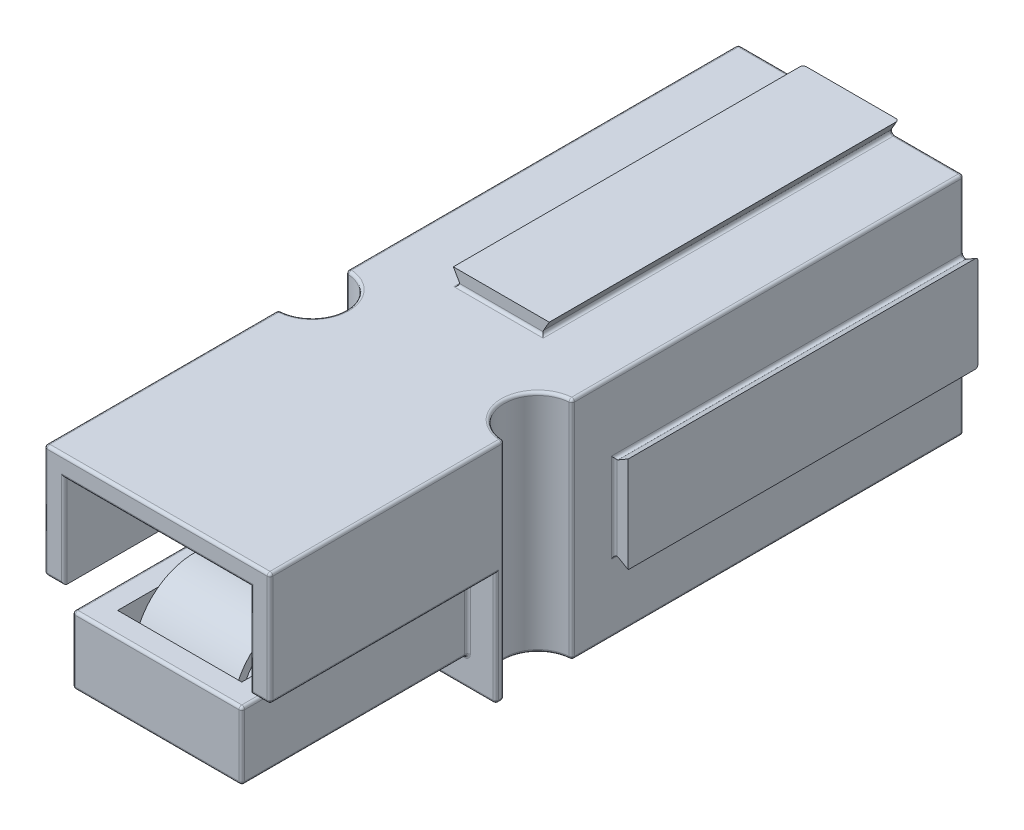
SolidWorks part; units mm, degrees
ref_plane "Face" through (0, 0, 0) normal (0, 0, 1) x (1, 0, 0)
ref_plane "Dessus" through (0, 0, 0) normal (0, 1, 0) x (1, 0, 0)
ref_plane "Droite" through (0, 0, 0) normal (1, 0, 0) x (0, 0, -1)
sketch "Esquisse1" plane through (0, 0, 0) normal (0, 0, 1) x (1, 0, 0)
  line L1 (-4.25, 4.25) -> (4.25, 4.25)
  line L2 (-4.25, 4.25) -> (-4.25, -4.25)
  line L3 (-4.25, -4.25) -> (4.25, -4.25)
  line L4 (4.25, 4.25) -> (4.25, -4.25)
  point P4 (0, 4.25)
  point P6 (-4.25, 0)
  dimension "D1" = 8.5
  dimension "D2" = 8.5
extrude "Extrusion1" add sketch "Esquisse1" along normal blind 24.6
sketch "Esquisse6" plane through (0, 0, 24.6) normal (0, 0, 1) x (1, 0, 0)
  line L0 (-4.25, 4.25) -> (-4.25, -4.25) construction
  line L2 (4.5005, 4.25) -> (4.5005, 3.75)
  line L3 (-4.25, 4.25) -> (-1.95, 4.25)
  line L4 (-4.25, 4.25) -> (-4.25, 3.75)
  line L5 (-4.25, 3.75) -> (-1.95, 3.75)
  line L6 (-1.95, 4.25) -> (-1.95, 3.75)
  line L7 (4.5005, 4.25) -> (1.45, 4.25)
  line L8 (1.45, 4.25) -> (1.45, 3.75)
  line L9 (4.5005, 3.75) -> (1.45, 3.75)
  dimension "D1" = 3.4
  dimension "D2" = 0.5
  dimension "D3" = 2.3
extrude "Enlèv. mat.-Extru.4" cut sketch "Esquisse6" against normal through all
sketch "Esquisse2" plane through (0, 0, 24.6) normal (0, 0, 1) x (1, 0, 0)
  line L0 (1.45, 4.25) -> (-1.95, 4.25) construction
  line L2 (-4.25, -4.25) -> (4.25, -4.25) construction
  line L8 (4.25, 1.45) -> (4.25, 4.25)
  line L12 (4.25, 4.25) -> (3.75, 4.25)
  line L13 (4.25, -4.25) -> (3.75, -4.25)
  line L14 (4.25, -4.25) -> (4.25, -1.95)
  line L15 (4.25, -1.95) -> (3.75, -1.95)
  line L16 (3.75, -4.25) -> (3.75, -1.95)
  line L18 (4.25, 1.45) -> (3.75, 1.45)
  line L19 (3.75, 4.25) -> (3.75, 1.45)
  dimension "D1" = 2.3
  dimension "D3" = 0.5
  dimension "D4" = 3.4
extrude "Enlèv. mat.-Extru.1" cut sketch "Esquisse2" against normal through all
sketch "Esquisse4" plane through (0, 3.75, 0) normal (0, 1, 0) x (-1, 0, 0)
  line L0 (0.25, 24.6) -> (0.25, 9.1927) construction
  line L6 (4.25, 24.6) -> (1.95, 24.6) construction
  circle A0 centre (-3.75, 15.1) radius 1.2
  circle A1 centre (4.25, 15.1) radius 1.2
  dimension "D1" = 2.4
  dimension "D2" = 9.5
extrude "Enlèv. mat.-Extru.3" cut sketch "Esquisse4" against normal through all
sketch "Esquisse11" plane through (0, 0, 24.6) normal (0, 0, 1) x (1, 0, 0)
  line L1 (-1.95, 4.25) -> (1.45, 4.25)
  line L2 (-1.95, 4.25) -> (-1.95, 3.75)
  line L3 (-1.95, 3.75) -> (1.45, 3.75)
  line L4 (1.45, 4.25) -> (1.45, 3.75)
  line L5 (4.25, 1.45) -> (3.75, 1.45)
  line L6 (4.25, 1.45) -> (4.25, -1.95)
  line L7 (4.25, -1.95) -> (3.75, -1.95)
  line L8 (3.75, 1.45) -> (3.75, -1.95)
extrude "Enlèv. mat.-Extru.9" cut sketch "Esquisse11" against normal blind 12.2
sketch "Esquisse5" plane through (0, 0, 24.6) normal (0, 0, 1) x (1, 0, 0)
  line L0 (-0.25, 3.75) -> (-0.25, -5.3524) construction
  line L1 (-4.25, -4.25) -> (3.75, -4.25) construction
  line L2 (-4.25, -0.25) -> (-3.25, -0.25)
  line L3 (-4.25, 3.75) -> (-4.25, -4.25) construction
  line L4 (-3.25, -0.25) -> (-3.25, -3.25)
  line L5 (-3.25, -3.25) -> (2.75, -3.25)
  line L6 (-4.25, 3.75) -> (3.75, 3.75) construction
  line L7 (-4.25, -0.25) -> (-4.25, -4.25)
  line L8 (-4.25, -4.25) -> (3.75, -4.25) construction
  line L9 (-4.25, -4.25) -> (3.75, -4.25) construction
  line L10 (2.75, -0.25) -> (2.75, -3.25)
  line L11 (3.75, -0.25) -> (2.75, -0.25)
  line L12 (3.75, -0.25) -> (3.75, -4.25)
  line L13 (-4.25, -4.25) -> (3.75, -4.25)
  point P19 (-0.25, -3.25)
  point P22 (-0.25, -4.25)
  dimension "D1" = 1
  dimension "D2" = 1
  dimension "D3" = 4
extrude "Enlèv. mat.-Extru.5" cut sketch "Esquisse5" against normal blind 8
sketch "Esquisse7" plane through (0, 0, 24.6) normal (0, 0, 1) x (1, 0, 0)
  line L5 (2.75, -0.85) -> (-3.25, -0.85)
  line L8 (-4.25, 3.05) -> (3.75, 3.05)
  line L9 (-3.55, 3.05) -> (3.05, 3.05)
  line L11 (-3.55, 3.75) -> (-3.55, -0.25)
  line L12 (3.05, -0.85) -> (-3.55, -0.85)
  line L24 (-3.55, 3.05) -> (-3.55, -0.85)
  line L26 (3.05, 3.75) -> (3.05, -0.25)
  line L27 (3.05, 3.05) -> (3.05, -0.85)
  dimension "D1" = 0.7
  dimension "D2" = 2.4
  dimension "D3" = 0.7
  dimension "D4" = 0.7
extrude "Enlèv. mat.-Extru.6" cut sketch "Esquisse7" against normal up to surface (8 mm away) up to face at (-0.25, -2, 16.6)
sketch "Esquisse8" plane through (0, 0, 0) normal (0, 0, -1) x (-1, 0, 0)
  line L37 (2.85, 3.75) -> (2.85, -4.25)
  line L38 (2.85, 2.35) -> (2.85, -2.85)
  line L40 (-2.35, -1.95) -> (-2.35, -4.25)
  line L41 (-2.35, 2.35) -> (-2.35, -2.85)
  line L43 (4.25, -2.85) -> (-3.75, -2.85)
  line L44 (2.85, -2.85) -> (-2.35, -2.85)
  line L46 (-1.45, 2.35) -> (-3.75, 2.35)
  line L47 (2.85, 2.35) -> (-2.35, 2.35)
  dimension "D1" = 1.4
  dimension "D2" = 1.4
  dimension "D3" = 1.4
  dimension "D4" = 1.4
extrude "Enlèv. mat.-Extru.7" cut sketch "Esquisse8" against normal blind 8
sketch "Esquisse9" plane through (0, 0, 0) normal (0, 0, -1) x (-1, 0, 0)
  line L0 (0.25, 4.25) -> (0.25, 3.6866) construction
  line L1 (-1.45, 4.25) -> (1.95, 4.25) construction
  line L2 (-1.45, 4.25) -> (-1.1613, 3.75)
  line L4 (-1.1613, 3.75) -> (-1.45, 3.75)
  line L5 (-1.45, 3.75) -> (-1.45, 4.25)
  line L6 (1.95, 3.75) -> (1.95, 4.25)
  line L7 (1.6613, 3.75) -> (1.95, 3.75)
  line L8 (1.95, 4.25) -> (1.6613, 3.75)
  line L9 (-4.25, -1.95) -> (-3.75, -1.95) construction
  line L10 (-4.25, 1.45) -> (-3.75, 1.1613)
  line L12 (-3.75, 1.1613) -> (-3.75, 1.45)
  line L13 (-3.75, 1.45) -> (-4.25, 1.45)
  line L14 (-3.75, -1.95) -> (-4.25, -1.95)
  line L15 (-3.75, -1.6613) -> (-3.75, -1.95)
  line L16 (-4.25, -1.95) -> (-3.75, -1.6613)
  dimension "D1" = 60
  dimension "D2" = 60
extrude "Enlèv. mat.-Extru.8" cut sketch "Esquisse9" against normal blind 13
sketch "Esquisse10" plane through (0, 0, 0) normal (0, 0, -1) x (-1, 0, 0)
  line L0 (4.25, -0.25) -> (-4.8932, -0.25) construction
  line L1 (4.25, 3.75) -> (4.25, -4.25) construction
sketch "Esquisse12" plane through (0, 0, 0) normal (0, 0, -1) x (-1, 0, 0)
  line L3 (4.25, 1.1613) -> (4.25, -1.6613)
  line L6 (4.25, -1.6613) -> (3.75, -1.95)
  line L7 (3.75, -1.95) -> (3.75, 1.45)
  line L8 (3.75, 1.45) -> (4.25, 1.1613)
  line L10 (-1.1613, -4.25) -> (1.6613, -4.25)
  line L13 (1.95, -3.75) -> (1.6613, -4.25)
  line L14 (-1.45, -3.75) -> (1.95, -3.75)
  line L15 (-1.1613, -4.25) -> (-1.45, -3.75)
extrude "Enlèv. mat.-Extru.10" cut sketch "Esquisse12" against normal up to surface (12.4 mm away) up to face at (-0.25, 4, 12.4)
ref_plane "Plan1" through (-0.25, 0, 0) normal (1, 0, 0) x (0, 0, -1)
sketch "Esquisse14" plane through (0, -0.85, 0) normal (0, 1, 0) x (-1, 0, 0)
  line L8 (2.45, 23.8) -> (-1.95, 23.8)
  line L9 (-1.95, 23.8) -> (-1.95, 17.4)
  line L10 (-1.95, 17.4) -> (2.45, 17.4)
  line L11 (2.45, 17.4) -> (2.45, 23.8)
  line L12 (2.45, 23.8) -> (-1.95, 23.8)
  line L13 (-1.95, 23.8) -> (-1.95, 17.4)
  line L14 (-1.95, 17.4) -> (2.45, 17.4)
  line L15 (2.45, 17.4) -> (2.45, 23.8)
  dimension "D1" = 0.8
extrude "Enlèv. mat.-Extru.11" cut sketch "Esquisse14" against normal blind 1.75
sketch "Esquisse13" plane through (-0.25, 0, 0) normal (1, 0, 0) x (0, 0, -1)
  line L0 (-20.6425, -0.1875) -> (-16.6, -1.3209)
  line L1 (-16.6, -4.25) -> (-16.6, -0.25) construction
  line L2 (-20.7474, -0.4697) -> (-16.6, -1.6325)
  line L3 (-23.2989, -1.5634) -> (-23.584, -1.4701)
  line L4 (-16.6, -1.6325) -> (-16.6, -1.3209)
  line L5 (-20.7474, -0.4697) -> (-16.681, -1.6098) construction
  arc A0 (-23.584, -1.4701) -> (-20.6425, -0.1875) centre (-21.5424, -2.1382) cw
  arc A1 (-23.2989, -1.5634) -> (-20.7474, -0.4697) centre (-21.5424, -2.1382) cw
  dimension "D1" = 0.3
extrude "Extrusion2" add sketch "Esquisse13" along normal blind 1.75 and the other way blind 1.75
sketch "Esquisse15" plane through (0, 0, 17.4) normal (0, 0, 1) x (1, 0, 0)
  line L4 (1.95, -0.85) -> (-2.45, -0.85)
  line L5 (-2.45, -0.85) -> (-2.45, -2.6)
  line L6 (-2.45, -2.6) -> (1.95, -2.6)
  line L7 (1.95, -2.6) -> (1.95, -0.85)
  line L8 (1.95, -0.85) -> (-2.45, -0.85)
  line L9 (-2.45, -0.85) -> (-2.45, -2.6)
  line L10 (-2.45, -2.6) -> (1.95, -2.6)
  line L11 (1.95, -2.6) -> (1.95, -0.85)
  dimension "D1" = 0
extrude "Enlèv. mat.-Extru.12" cut sketch "Esquisse15" against normal up to surface (0.8 mm away) up to face at (-0.25, -0.425, 16.6)
sketch "Esquisse16" plane through (0, 0, 0) normal (0, 0, -1) x (-1, 0, 0)
  line L0 (0.25, 2.35) -> (0.25, -2.85) construction
  line L1 (2.85, 2.35) -> (-2.35, 2.35) construction
  line L2 (-2.35, -2.85) -> (2.85, -2.85) construction
  line L3 (2.85, -0.25) -> (-2.35, -0.25) construction
  line L4 (2.85, -2.85) -> (2.85, 2.35) construction
  line L5 (4.25, -0.25) -> (-4.8932, -0.25) construction
  circle A0 centre (0.25, -0.25) radius 2.6
fillet "Fillet1" radius 0.1 70 edges at (1.1613, -4.25, 6.2) (-1.8057, 4, 0) (4, 1.3057, 0) (3.75, -1.6613, 6.2) (4, -1.8057, 0) (-4.25, -0.25, 12.4) (2.4557, -4.25, 0) (-4.25, 1.1613, 6.2) (-0.25, -4.25, 12.4) (3.75, -4.25, 6.95) (-1.6613, -4.25, 6.2) (2.55, -4.25, 15.1) (3.75, -4.25, 16.45) (-4.25, -4.25, 16.45) (-3.05, -4.25, 15.1) (-4.25, -4.25, 6.95) (-2.9557, -4.25, 0) (-4.25, -1.6613, 6.2) (-4.25, -2.9557, 0) (-4.25, -0.25, 13.9) (-4.25, 2.4557, 0) (3.75, 1.75, 24.6) (3.75, -0.25, 16.3) (-4.25, -0.25, 20.6) (-4.25, -0.25, 16.3) (-2.9557, 3.75, 0) (2.4557, 3.75, 0) (3.75, 2.4557, 0) (3.75, -2.9557, 0) (-1.6613, 3.75, 6.2) (-4.25, 3.75, 6.95) (-3.05, 3.75, 15.1) (-4.25, 3.75, 20.45) (-0.25, 3.75, 24.6) (3.75, 3.75, 20.45) (3.75, 3.75, 6.95) (3.75, 1.1613, 6.2) (3.75, -0.25, 13.9) (2.55, 3.75, 15.1) (-0.25, 3.75, 12.4) (3.75, -0.25, 12.4) (-3.9, -0.25, 24.6) (-3.25, -2.05, 24.6) (-3.25, -0.85, 20.6) (-3.25, -3.25, 20.6) (-0.25, -3.25, 24.6) (2.75, -3.25, 20.6) (2.75, -0.85, 20.6) (2.75, -2.05, 24.6) (3.4, -0.25, 24.6) (3.75, -0.25, 20.6) (-4.25, -2.25, 16.6) (-0.25, -4.25, 16.6) (3.75, -2.25, 16.6) (2.75, -2.05, 16.6) (-0.25, -3.25, 16.6) (-3.25, -2.05, 16.6) (-3.55, 1.4, 24.6) (3.05, 1.4, 24.6) (2.35, -0.85, 16.6) (-2.85, -0.85, 16.6) (-0.25, -0.85, 24.6) (-0.25, 3.05, 24.6) (-0.25, 2.35, 0) (-2.85, -0.25, 0) (-0.25, -2.85, 0) (-4.25, 1.75, 24.6) (2.35, -0.25, 0) (1.1613, 3.75, 6.2) (1.3057, 4, 0)
sketch "Sketch1" plane through (0, 0, 8) normal (0, 0, -1) x (-1, 0, 0)
  line L0 (0.25, -0.25) -> (0.25, 2.35) construction
  line L1 (2.85, 2.35) -> (-2.35, 2.35) construction
  line L2 (0.25, -0.25) -> (2.85, -0.25) construction
  line L3 (2.85, -2.85) -> (2.85, 2.35) construction
  line L4 (0.25, -0.25) -> (0.25, -2.85) construction
  line L5 (-2.35, -2.85) -> (2.85, -2.85) construction
  line L6 (0.25, -0.25) -> (-2.35, -0.25) construction
  line L7 (-2.35, 2.35) -> (-2.35, -2.85) construction
  circle A0 centre (0.25, -0.25) radius 2
  dimension "D1" = 4
extrude "Cut-Extrude1" cut sketch "Sketch1" against normal offset from surface (7.6 mm away) 1 up to face at (-0.25, -0.4, 16.6)
